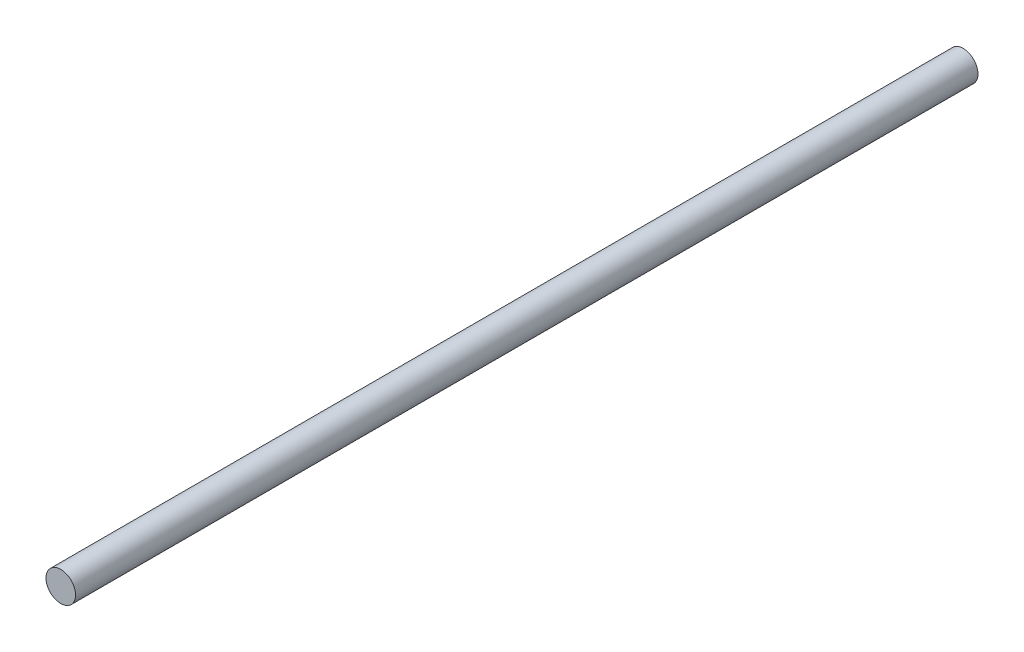
SolidWorks part; units mm, degrees
material "Plain Carbon Steel"
ref_plane "Front Plane" through (0, 0, 0) normal (0, 0, 1) x (1, 0, 0)
ref_plane "Top Plane" through (0, 0, 0) normal (0, 1, 0) x (1, 0, 0)
ref_plane "Right Plane" through (0, 0, 0) normal (1, 0, 0) x (0, 0, -1)
sketch "Sketch1" plane through (0, 0, 0) normal (0, 0, 1) x (1, 0, 0)
  circle A0 centre (0, 0) radius 5
  dimension "D1" = 10
extrude "Boss-Extrude1" add sketch "Sketch1" along normal blind 305
